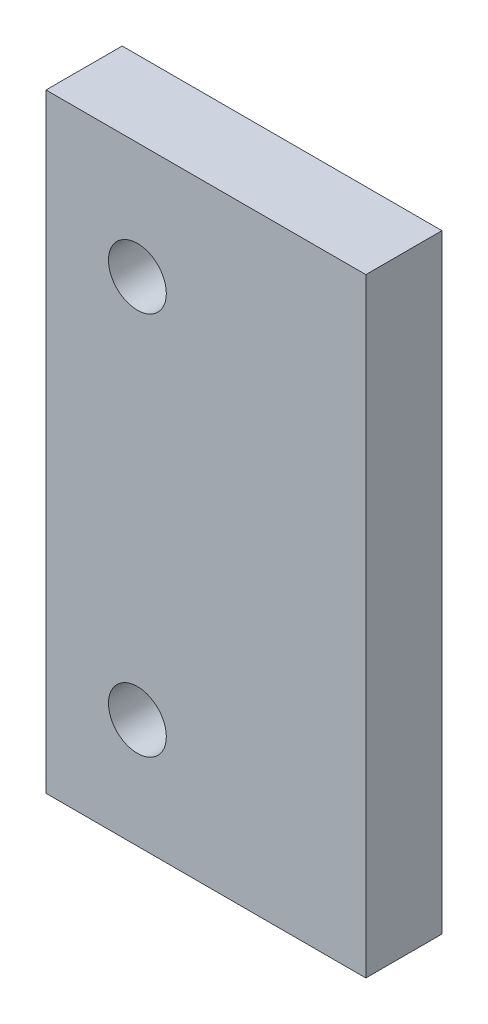
SolidWorks part; units mm, degrees
ref_plane "Front Plane" through (0, 0, 0) normal (0, 0, 1) x (1, 0, 0)
ref_plane "Top Plane" through (0, 0, 0) normal (0, 1, 0) x (1, 0, 0)
ref_plane "Right Plane" through (0, 0, 0) normal (1, 0, 0) x (0, 0, -1)
sketch "Sketch2" plane through (0, 0, 0) normal (0, 0, 1) x (1, 0, 0)
  line L0 (0, 0) -> (0, 20)
  line L1 (0, 20) -> (10.5, 20)
  line L2 (10.5, 20) -> (10.5, 0)
  line L3 (10.5, 0) -> (0, 0)
  dimension "D1" = 10.5
  dimension "D2" = 20
extrude "Boss-Extrude1" add sketch "Sketch2" along normal blind 2.5
sketch "Sketch3" plane through (0, 0, 2.5) normal (0, 0, 1) x (1, 0, 0)
  line L0 (0, 20) -> (0, 0) construction
  circle A0 centre (3, 16.1883) radius 0.95
  circle A1 centre (3, 3.5883) radius 0.95
  dimension "D1" = 3
  dimension "D2" = 3
  dimension "D5" = 1.9
  dimension "D6" = 1.9
  dimension "D7" = 12.6
extrude "Cut-Extrude1" cut sketch "Sketch3" against normal through all
